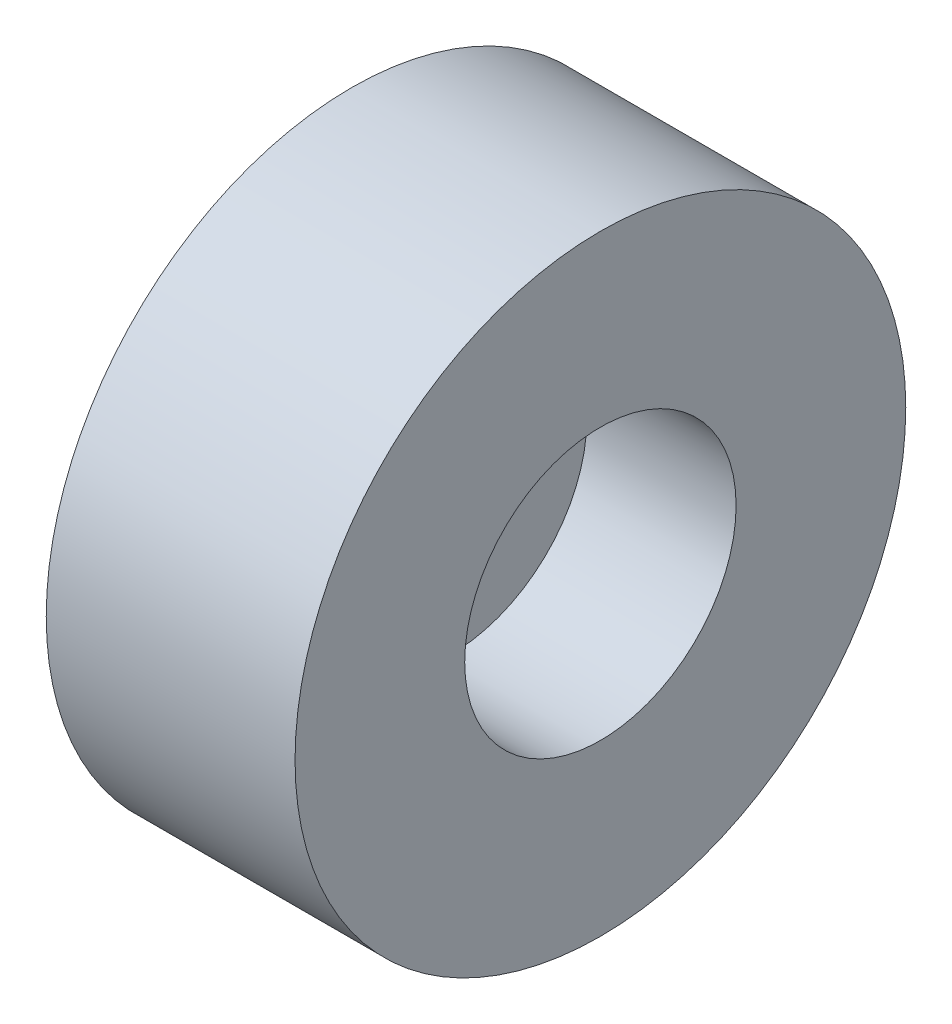
SolidWorks part; units mm, degrees
ref_plane "Front Plane" through (0, 0, 0) normal (0, 0, 1) x (1, 0, 0)
ref_plane "Top Plane" through (0, 0, 0) normal (0, 1, 0) x (1, 0, 0)
ref_plane "Right Plane" through (0, 0, 0) normal (1, 0, 0) x (0, 0, -1)
sketch "Sketch1" plane through (0, 0, 0) normal (1, 0, 0) x (0, 0, -1)
  circle A0 centre (0, 0) radius 6.75
extrude "Boss-Extrude1" add sketch "Sketch1" along normal blind 5.5
sketch "Sketch2" plane through (5.5, 0, 0) normal (1, 0, 0) x (0, 0, -1)
  circle A0 centre (0, 0) radius 3
extrude "Cut-Extrude1" cut sketch "Sketch2" against normal blind 3.3
sketch "Sketch3" plane through (2.2, 0, 0) normal (1, 0, 0) x (0, 0, -1)
  circle A0 centre (0, 0) radius 1.5
extrude "Cut-Extrude2" cut sketch "Sketch3" against normal blind 3.3
